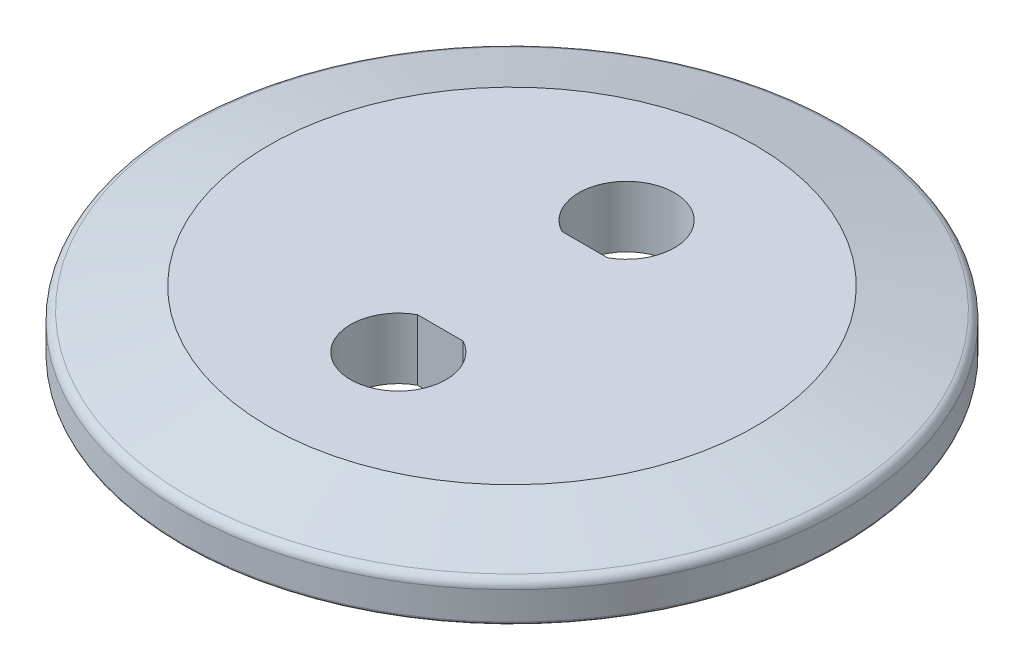
SolidWorks part; units mm, degrees
material "AISI 304"
ref_plane "Front Plane" through (0, 0, 0) normal (0, 0, 1) x (1, 0, 0)
ref_plane "Top Plane" through (0, 0, 0) normal (0, 1, 0) x (1, 0, 0)
ref_plane "Right Plane" through (0, 0, 0) normal (1, 0, 0) x (0, 0, -1)
sketch "Sketch1" plane through (0, 0, 0) normal (1, 0, 0) x (0, 0, -1)
  line L0 (0, 0) -> (0, 5.1) construction
  line L1 (-27.5, 0) -> (-27.5, 3.175)
  line L2 (-27.5, 3.175) -> (-20.3158, 5.1)
  line L6 (0, 2.5) -> (-20.625, 2.5)
  line L7 (-20.625, 2.5) -> (-20.625, 0)
  line L8 (-20.625, 0) -> (-27.5, 0)
  line L9 (-20.3158, 5.1) -> (0, 5.1)
  line L10 (0, 5.1) -> (0, 2.5)
  dimension "D1" = 75
  dimension "D2" = 40.6316
  dimension "Flange ID" = 41.25
  dimension "Flange OD" = 55
  dimension "D5" = 3.175
  dimension "Flange Height" = 5.1
  dimension "D9" = 2.5
revolve "Flange" add sketch "Sketch1" angle 360 about L0
sketch "Sketch2" plane through (0, 0, 0) normal (1, 0, 0) x (0, 0, -1)
  line L0 (0, 2.5) -> (-20.625, 2.5) construction
  line L1 (0, 0) -> (-15.85, 0)
  line L2 (0, 0) -> (0, 2.5)
  line L3 (0, 2.5) -> (-15.85, 2.5)
  line L4 (-15.85, 0) -> (-15.85, 2.5)
  line L5 (0, 0) -> (0, -4.8376) construction
  dimension "ID" = 31.7
revolve "Blank Insert" add sketch "Sketch2" angle 360 about L5
ref_plane "Plane1" through (0, -1.905, 0) normal (0, -1, 0) x (-1, 0, 0)
ref_plane "Plane2" through (0, 2.5, 0) normal (0, -1, 0) x (-1, 0, 0)
ref_plane "Plane3" through (0, 5.1, 0) normal (0, -1, 0) x (-1, 0, 0)
fillet "Fillet1" radius 0.762 1 edges at (0, 3.175, -27.5)
fillet "Fillet2" radius 0.254 1 edges at (0, 0, -27.5)
sketch "Sketch3" plane through (0, 5.1, 0) normal (0, 1, 0) x (1, 0, 0)
  line L0 (-1.8625, 6.0198) -> (1.9407, 6.0198)
  arc A0 (1.9407, 6.0198) -> (-1.8625, 6.0198) centre (0.0391, 9.525) ccw
  dimension "D3" = 3.9878
  dimension "D1" = 3.5052
  dimension "D2" = 9.525
extrude "Cut-Extrude1" cut sketch "Sketch3" against normal through all
mirror "Mirror1" about plane through (0, 0, 0) normal (0, 0, 1) of "Cut-Extrude1"
